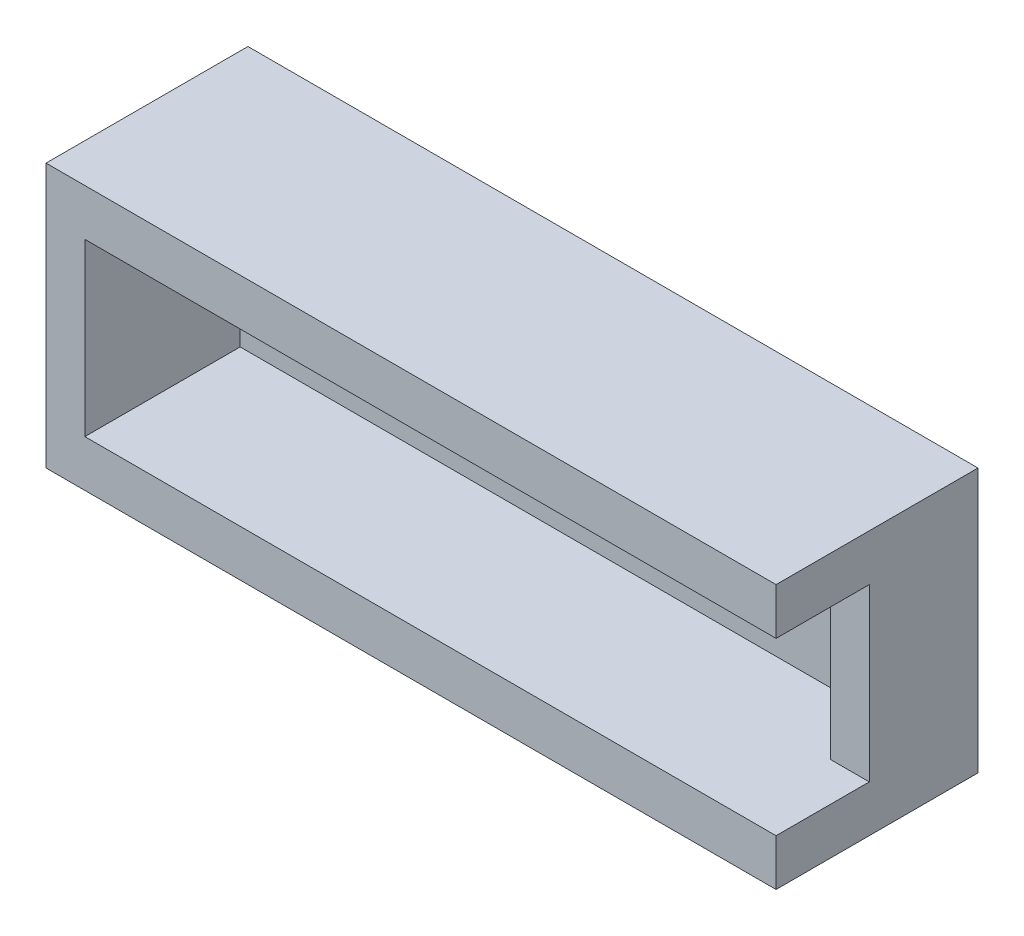
SolidWorks part; units mm, degrees
ref_plane "前基準面" through (0, 0, 0) normal (0, 0, 1) x (1, 0, 0)
ref_plane "上基準面" through (0, 0, 0) normal (0, 1, 0) x (1, 0, 0)
ref_plane "右基準面" through (0, 0, 0) normal (1, 0, 0) x (0, 0, -1)
sketch "草圖1" plane through (0, 0, 0) normal (0, 0, 1) x (1, 0, 0)
  line L1 (-15.0064, 10.2976) -> (31.9936, 10.2976)
  line L2 (-15.0064, 10.2976) -> (-15.0064, -6.7024)
  line L3 (-15.0064, -6.7024) -> (31.9936, -6.7024)
  line L4 (31.9936, 10.2976) -> (31.9936, -6.7024)
  line L5 (-12.5064, 7.2976) -> (29.4936, 7.2976)
  line L6 (-12.5064, 7.2976) -> (-12.5064, -3.7024)
  line L7 (-12.5064, -3.7024) -> (29.4936, -3.7024)
  line L8 (29.4936, 7.2976) -> (29.4936, -3.7024)
  dimension "D1" = 47
  dimension "D2" = 17
  dimension "D3" = 42
  dimension "D4" = 2.5
  dimension "D5" = 11
  dimension "D6" = 3
extrude "填料-伸長1" add sketch "草圖1" along normal blind 10
sketch "草圖2" plane through (0, 0, 0) normal (0, 0, -1) x (-1, 0, 0)
  line L1 (15.0064, -6.7024) -> (-31.9936, -6.7024)
  line L2 (15.0064, -6.7024) -> (15.0064, 10.2976)
  line L3 (15.0064, 10.2976) -> (-31.9936, 10.2976)
  line L4 (-31.9936, -6.7024) -> (-31.9936, 10.2976)
extrude "填料-伸長2" add sketch "草圖2" along normal blind 3
sketch "草圖3" plane through (31.9936, 0, 0) normal (1, 0, 0) x (0, 0, -1)
  line L0 (-10, -6.7024) -> (-10, 10.2976) construction
  line L1 (-10, -3.7024) -> (-4, -3.7024)
  line L2 (-10, -3.7024) -> (-10, 7.2976)
  line L3 (-10, 7.2976) -> (-4, 7.2976)
  line L4 (-4, -3.7024) -> (-4, 7.2976)
  line L5 (-10, -6.7024) -> (3, -6.7024) construction
  line L6 (-10, 10.2976) -> (3, 10.2976) construction
  dimension "D1" = 3
  dimension "D2" = 6
  dimension "D3" = 3
extrude "除料-伸長2" cut sketch "草圖3" against normal blind 3
